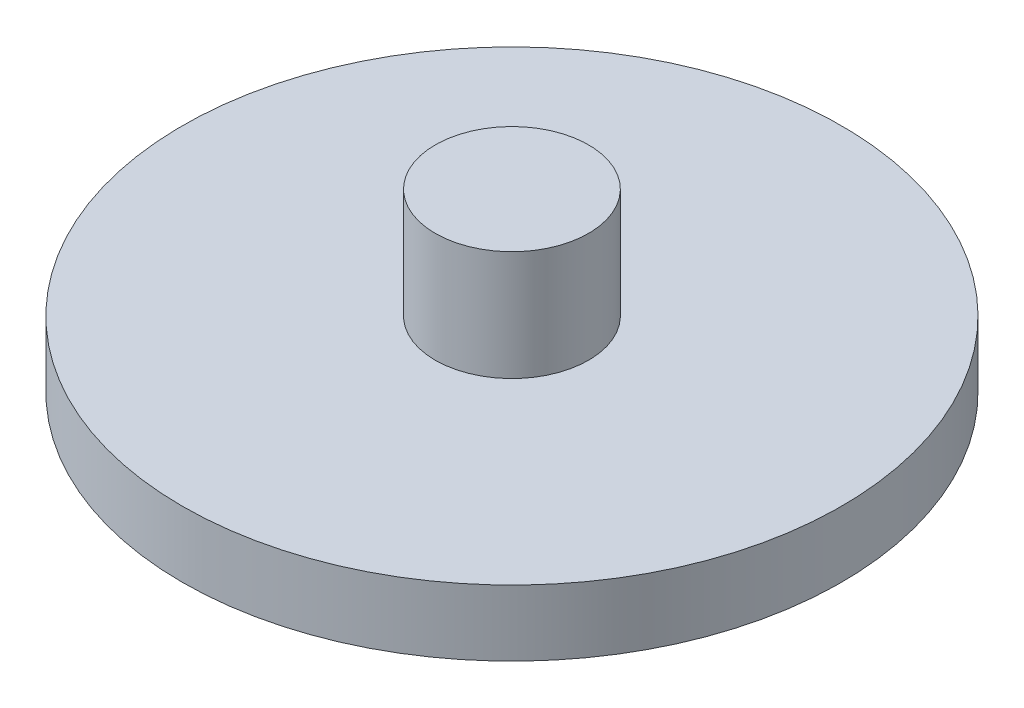
SolidWorks part; units mm, degrees
ref_plane "Front Plane" through (0, 0, 0) normal (0, 0, 1) x (1, 0, 0)
ref_plane "Top Plane" through (0, 0, 0) normal (0, 1, 0) x (1, 0, 0)
ref_plane "Right Plane" through (0, 0, 0) normal (1, 0, 0) x (0, 0, -1)
sketch "Sketch1" plane through (0, 0, 0) normal (0, 1, 0) x (1, 0, 0)
  circle A0 centre (0, 0) radius 15
  dimension "D1" = 30
extrude "Boss-Extrude1" add sketch "Sketch1" along normal blind 3
sketch "Sketch2" plane through (0, 3, 0) normal (0, 1, 0) x (1, 0, 0)
  circle A0 centre (0, 0) radius 3.49
  dimension "D1" = 6.98
extrude "Boss-Extrude2" add sketch "Sketch2" along normal blind 5
